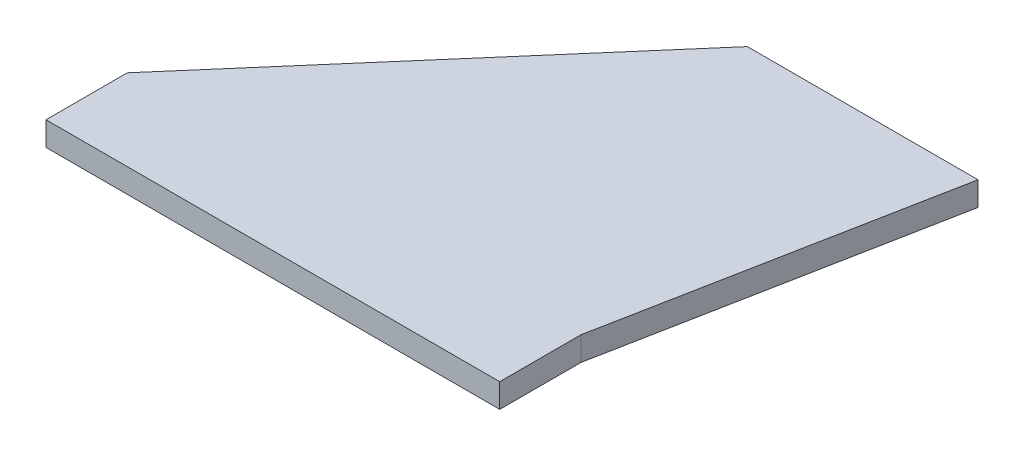
SolidWorks part; units mm, degrees
ref_plane "Front Plane" through (0, 0, 0) normal (0, 0, 1) x (1, 0, 0)
ref_plane "Top Plane" through (0, 0, 0) normal (0, 1, 0) x (1, 0, 0)
ref_plane "Right Plane" through (0, 0, 0) normal (1, 0, 0) x (0, 0, -1)
sketch "Sketch1" plane through (0, 0, 0) normal (0, 1, 0) x (1, 0, 0)
  line L0 (-120, 0) -> (0, 0)
  line L1 (0, 0) -> (17, 88)
  line L2 (17, 88) -> (-44, 88)
  line L3 (-44, 88) -> (-120, 0)
  line L4 (-120, 0) -> (-120, 83.9707) construction
  dimension "D1" = 120
  dimension "D2" = 61
  dimension "D3" = 88
  dimension "D4" = 49.185
  dimension "D5" = 76
  dimension "D6" = 40.815
extrude "Boss-Extrude1" add sketch "Sketch1" along normal blind 6.35
sketch "Sketch3" plane through (0, 0, 0) normal (0, 1, 0) x (1, 0, 0)
  line L0 (-120, 0) -> (-120, -21.5)
  line L1 (-120, -21.5) -> (0, -21.5)
  line L2 (0, -21.5) -> (0, 0)
  line L3 (0, 0) -> (-120, 0)
  dimension "D1" = 21.5
extrude "Boss-Extrude2" add sketch "Sketch3" along normal blind 6.35
